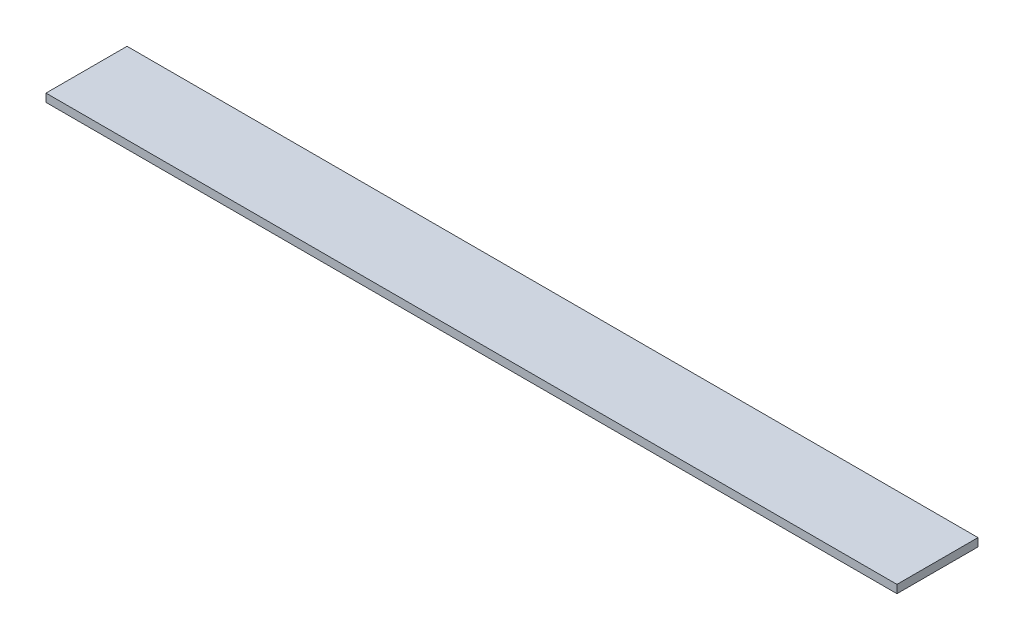
SolidWorks part; units mm, degrees
ref_plane "Face" through (0, 0, 0) normal (0, 0, 1) x (1, 0, 0)
ref_plane "Dessus" through (0, 0, 0) normal (0, 1, 0) x (1, 0, 0)
ref_plane "Droite" through (0, 0, 0) normal (1, 0, 0) x (0, 0, -1)
sketch "Esquisse1" plane through (0, 0, 0) normal (0, 1, 0) x (1, 0, 0)
  line L1 (0, 0) -> (1050, 0)
  line L2 (0, 0) -> (0, 100)
  line L3 (0, 100) -> (1050, 100)
  line L4 (1050, 0) -> (1050, 100)
  dimension "D1" = 1050
  dimension "D2" = 100
extrude "Extrusion1" add sketch "Esquisse1" along normal blind 10
